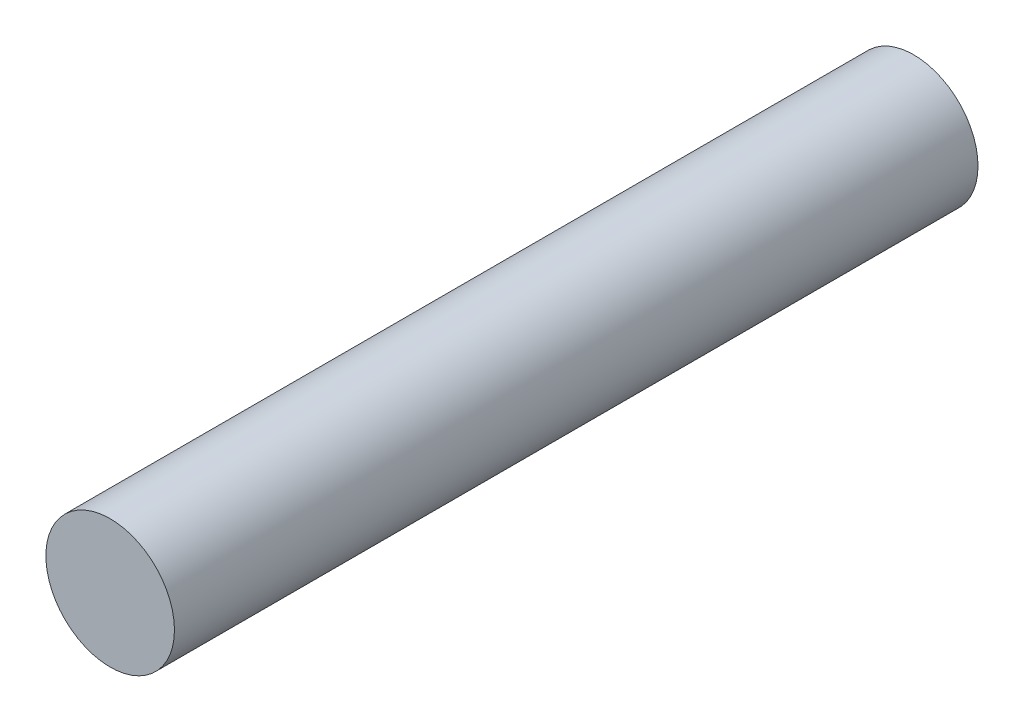
SolidWorks part; units mm, degrees
material "Plain Carbon Steel"
ref_plane "Front Plane" through (0, 0, 0) normal (0, 0, 1) x (1, 0, 0)
ref_plane "Top Plane" through (0, 0, 0) normal (0, 1, 0) x (1, 0, 0)
ref_plane "Right Plane" through (0, 0, 0) normal (1, 0, 0) x (0, 0, -1)
sketch "Sketch2" plane through (0, 0, 0) normal (0, 0, 1) x (1, 0, 0)
  circle A0 centre (0, 0) radius 1.016
  dimension "D1" = 2.032
extrude "Boss-Extrude1" add sketch "Sketch2" along normal mid plane 12.7
